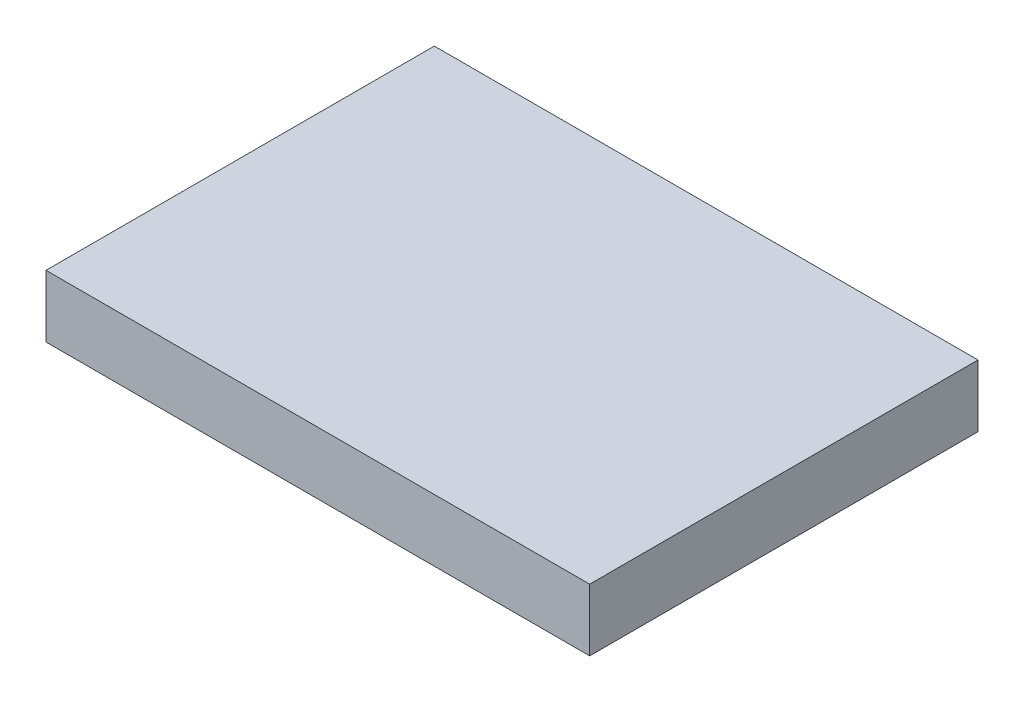
SolidWorks part; units mm, degrees
ref_plane "前视基准面" through (0, 0, 0) normal (0, 0, 1) x (1, 0, 0)
ref_plane "上视基准面" through (0, 0, 0) normal (0, 1, 0) x (1, 0, 0)
ref_plane "右视基准面" through (0, 0, 0) normal (1, 0, 0) x (0, 0, -1)
sketch "草图1" plane through (0, 0, 0) normal (0, 1, 0) x (1, 0, 0)
  line L1 (-8.75, 6.25) -> (8.75, 6.25)
  line L2 (-8.75, 6.25) -> (-8.75, -6.25)
  line L3 (-8.75, -6.25) -> (8.75, -6.25)
  line L4 (8.75, 6.25) -> (8.75, -6.25)
  line L5 (-8.75, 6.25) -> (8.75, -6.25) construction
  line L6 (-8.75, -6.25) -> (8.75, 6.25) construction
  point P0 (0, 0)
  dimension "D1" = 12.5
  dimension "D2" = 17.5
extrude "凸台-拉伸1" add sketch "草图1" along normal blind 2
